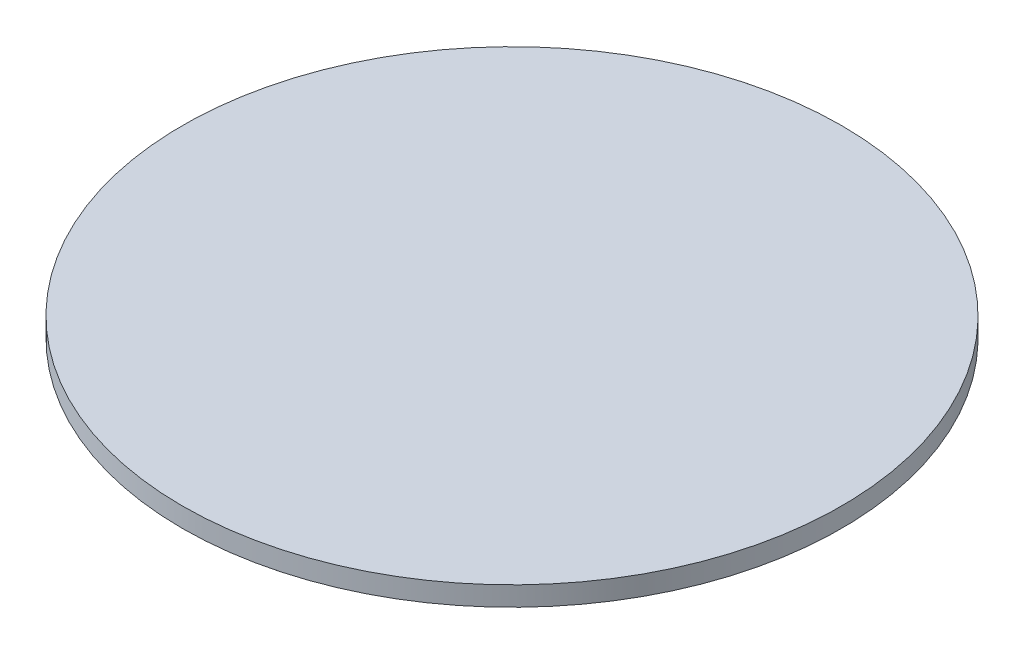
SolidWorks part; units mm, degrees
ref_plane "前视基准面" through (0, 0, 0) normal (0, 0, 1) x (1, 0, 0)
ref_plane "上视基准面" through (0, 0, 0) normal (0, 1, 0) x (1, 0, 0)
ref_plane "右视基准面" through (0, 0, 0) normal (1, 0, 0) x (0, 0, -1)
sketch "草图1" plane through (0, 0, 0) normal (0, 1, 0) x (1, 0, 0)
  circle A0 centre (0, 0) radius 25.4
  dimension "D1" = 50.8
extrude "凸台-拉伸1" add sketch "草图1" along normal blind 1.5
